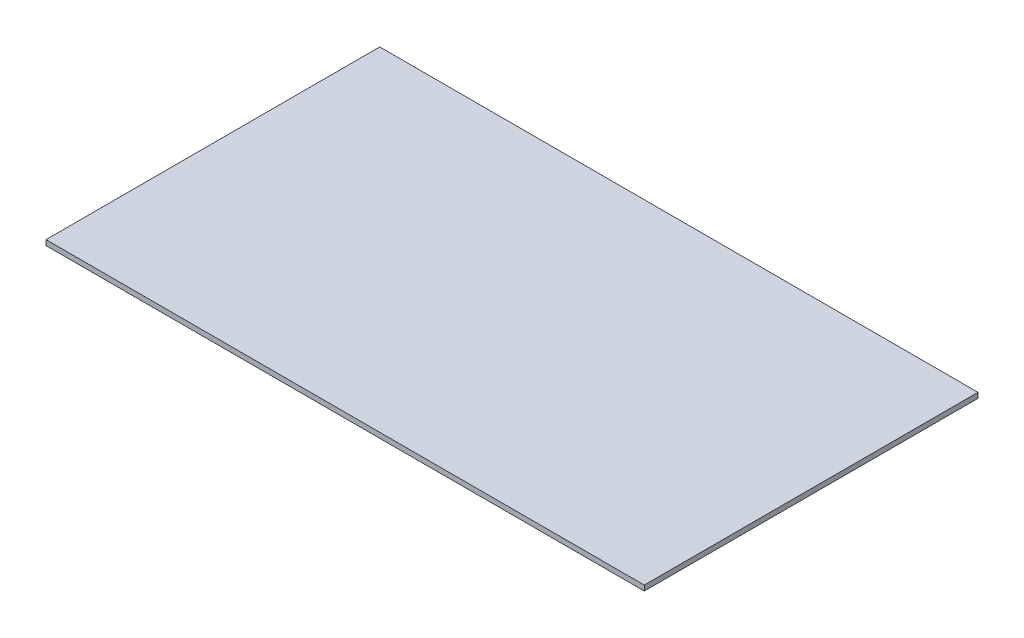
SolidWorks part; units mm, degrees
material "Pine"
ref_plane "Front Plane" through (0, 0, 0) normal (0, 0, 1) x (1, 0, 0)
ref_plane "Top Plane" through (0, 0, 0) normal (0, 1, 0) x (1, 0, 0)
ref_plane "Right Plane" through (0, 0, 0) normal (1, 0, 0) x (0, 0, -1)
sketch "Sketch1" plane through (0, 0, 0) normal (0, 1, 0) x (1, 0, 0)
  line L1 (-1092.87, 609.6) -> (1092.87, 609.6)
  line L2 (-1092.87, 609.6) -> (-1092.87, -609.6)
  line L3 (-1092.87, -609.6) -> (1092.87, -609.6)
  line L4 (1092.87, 609.6) -> (1092.87, -609.6)
  line L5 (-1092.87, 609.6) -> (1092.87, -609.6) construction
  line L6 (-1092.87, -609.6) -> (1092.87, 609.6) construction
  point P0 (0, 0)
  dimension "D1" = 1219.2
  dimension "D2" = 2185.74
extrude "Boss-Extrude1" add sketch "Sketch1" along normal blind 19.05
